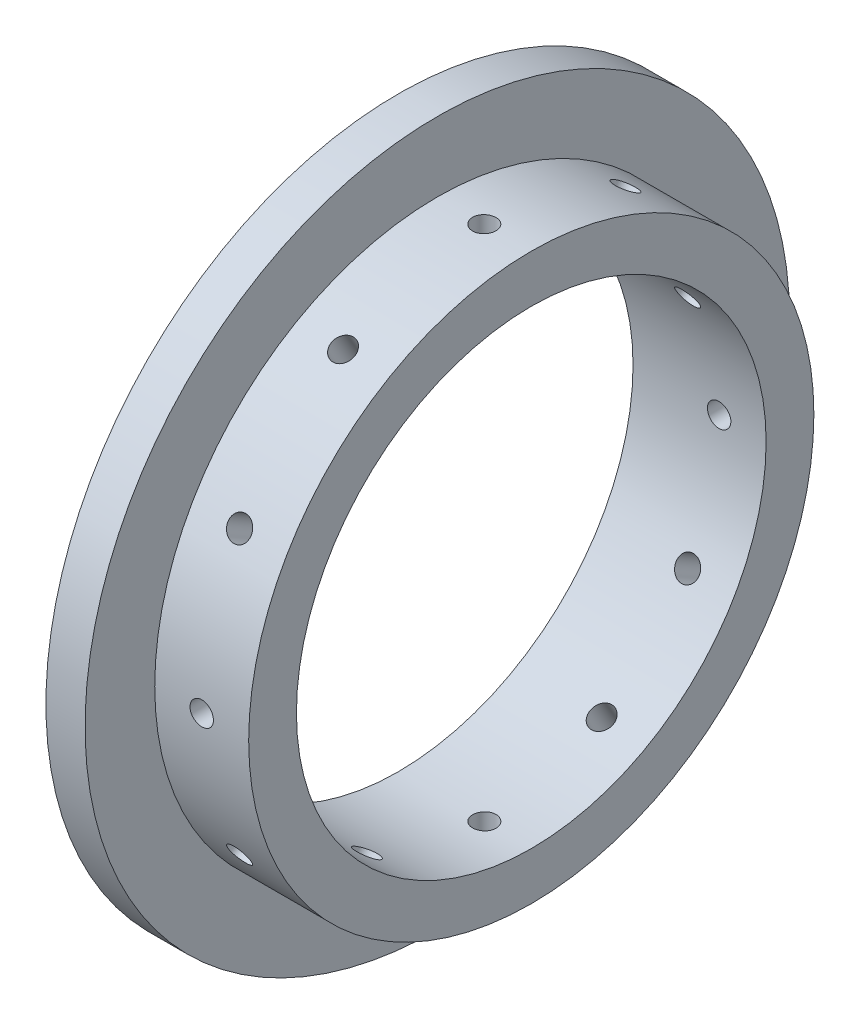
SolidWorks part; units mm, degrees
material "AISI 304"
ref_plane "Front Plane" through (0, 0, 0) normal (0, 0, 1) x (1, 0, 0)
ref_plane "Top Plane" through (0, 0, 0) normal (0, 1, 0) x (1, 0, 0)
ref_plane "Right Plane" through (0, 0, 0) normal (1, 0, 0) x (0, 0, -1)
sketch "Sketch1" plane through (0, 0, 0) normal (1, 0, 0) x (0, 0, -1)
  circle A0 centre (0, 0) radius 38.1
  circle A1 centre (0, 0) radius 57.15
  dimension "D1" = 76.2
  dimension "D2" = 114.3
extrude "Boss-Extrude1" add sketch "Sketch1" along normal blind 6.35
sketch "Sketch2" plane through (6.35, 0, 0) normal (1, 0, 0) x (0, 0, -1)
  circle A0 centre (0, 0) radius 45.847
  circle A1 centre (0, 0) radius 38.1
  dimension "D1" = 91.694
  dimension "D2" = 76.2
extrude "Boss-Extrude2" add sketch "Sketch2" along normal blind 15.24
sketch "Sketch3" plane through (0, 0, 0) normal (0, 1, 0) x (1, 0, 0)
  line L0 (0, 0) -> (88.5884, 0) construction
  line L1 (-13.97, 0) -> (13.97, 0) construction
  line L2 (0, 0) -> (0, 82.8947) construction
ref_plane "Plane1" through (0, 0, -45.847) normal (0, 0, -1) x (-1, 0, 0)
sketch "Sketch4" plane through (0, 0, -45.847) normal (0, 0, -1) x (-1, 0, 0)
  line L0 (0, 0) -> (-88.5884, 0) construction
  line L2 (-6.35, 45.847) -> (-6.35, -45.847) construction
  circle A0 centre (-13.97, 0) radius 1.8986
  dimension "D2" = 3.7973
  dimension "D1" = 7.62
extrude "Cut-Extrude1" cut sketch "Sketch4" against normal blind 11.43
pattern_circular "CirPattern1" count 12 over 360 about axis through (0, 0, 0) along (1, 0, 0) of "Cut-Extrude1"
